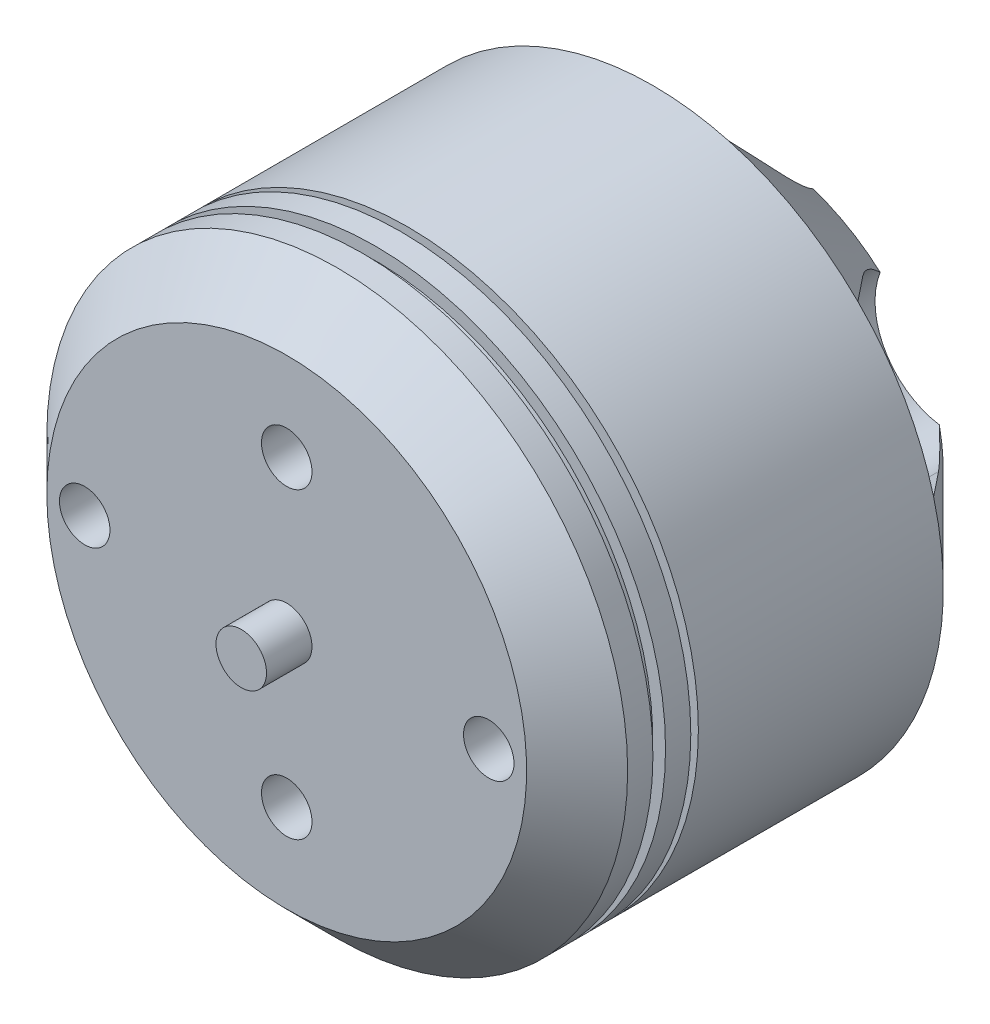
SolidWorks part; units mm, degrees
ref_plane "Front Plane" through (0, 0, 0) normal (0, 0, 1) x (1, 0, 0)
ref_plane "Top Plane" through (0, 0, 0) normal (0, 1, 0) x (1, 0, 0)
ref_plane "Right Plane" through (0, 0, 0) normal (1, 0, 0) x (0, 0, -1)
sketch "Sketch2" plane through (0, 0, 0) normal (0, 1, 0) x (1, 0, 0)
  line L0 (0, 22) -> (0, -1.8)
  line L1 (0, -1.8) -> (1, -1.8)
  line L2 (1, -1.8) -> (1, 0)
  line L3 (1, 0) -> (9.5, 0)
  line L4 (9.5, 0) -> (11.5, 2)
  line L5 (11.5, 2) -> (11.5, 3)
  line L6 (11.5, 14.5) -> (7.5, 18.5)
  line L7 (7.5, 18.5) -> (1, 18.5)
  line L8 (1, 18.5) -> (1, 22)
  line L9 (1, 22) -> (0, 22)
  line L10 (2, 17.5) -> (7.0858, 17.5)
  line L11 (7.0858, 17.5) -> (10.5, 14.0858)
  line L12 (10.5, 14.0858) -> (10.5, 8.9941)
  line L13 (10.5, 8.9941) -> (1, 8.9941)
  line L14 (1, 8.9941) -> (1, 16.5)
  line L15 (1, 16.5) -> (2, 16.5)
  line L16 (2, 16.5) -> (2, 17.5)
  line L17 (11.5, 3) -> (11, 3)
  line L18 (11, 3) -> (11, 3.5)
  line L19 (11, 3.5) -> (11.5, 3.5)
  line L20 (11.5, 4.5) -> (9.5, 4.5)
  line L21 (9.5, 4.5) -> (9.5, 4.8)
  line L22 (9.5, 4.8) -> (11.5, 4.8)
  line L23 (11.5, 4.8) -> (11.5, 14.5)
  line L24 (11.5, 3.5) -> (11.5, 4.5)
  dimension "D1" = 23.8
  dimension "D2" = 1.8
  dimension "D3" = 45
  dimension "D4" = 2
  dimension "D5" = 11.5
  dimension "D6" = 1
  dimension "D7" = 1
  dimension "D8" = 45
  dimension "D9" = 3.5
  dimension "D10" = 1
  dimension "D11" = 1
  dimension "D12" = 1
  dimension "D13" = 1
  dimension "D14" = 1
  dimension "D15" = 1
  dimension "D16" = 4
  dimension "D17" = 0.5
  dimension "D18" = 0.5
  dimension "D19" = 0.3
  dimension "D20" = 2
  dimension "D21" = 1
  dimension "D22" = 1
  dimension "D23" = 8.9941
revolve "Revolve3" add sketch "Sketch2" angle 360 about L0
sketch "Sketch3" plane through (0, 0, -18.5) normal (0, 0, -1) x (-1, 0, 0)
  line L0 (0, 0) -> (0, 9) construction
  line L1 (-3, 9) -> (-3, 16.3813)
  line L2 (-3, 16.3813) -> (3, 16.3813)
  line L3 (3, 16.3813) -> (3, 9)
  line L4 (15.6866, 5.5926) -> (9.2942, 1.9019)
  line L5 (12.6866, 10.7887) -> (15.6866, 5.5926)
  line L6 (6.2942, 7.0981) -> (12.6866, 10.7887)
  line L7 (12.6866, -10.7887) -> (6.2942, -7.0981)
  line L8 (15.6866, -5.5926) -> (12.6866, -10.7887)
  line L9 (9.2942, -1.9019) -> (15.6866, -5.5926)
  line L10 (-3, -16.3813) -> (-3, -9)
  line L11 (3, -16.3813) -> (-3, -16.3813)
  line L12 (3, -9) -> (3, -16.3813)
  line L13 (-15.6866, -5.5926) -> (-9.2942, -1.9019)
  line L14 (-12.6866, -10.7887) -> (-15.6866, -5.5926)
  line L15 (-6.2942, -7.0981) -> (-12.6866, -10.7887)
  line L16 (-12.6866, 10.7887) -> (-6.2942, 7.0981)
  line L17 (-15.6866, 5.5926) -> (-12.6866, 10.7887)
  line L18 (-9.2942, 1.9019) -> (-15.6866, 5.5926)
  circle A0 centre (0, 0) radius 4.5 construction
  circle A1 centre (0, 4.5) radius 1
  circle A2 centre (0, 0) radius 4.5 construction
  circle A3 centre (4.5, 0) radius 1
  circle A4 centre (0, 0) radius 4.5 construction
  circle A5 centre (0, -4.5) radius 1
  circle A6 centre (0, 0) radius 4.5 construction
  circle A7 centre (-4.5, 0) radius 1
  arc A8 (-3, 9) -> (3, 9) centre (0, 9) ccw
  arc A9 (6.2942, 7.0981) -> (9.2942, 1.9019) centre (7.7942, 4.5) ccw
  arc A10 (9.2942, -1.9019) -> (6.2942, -7.0981) centre (7.7942, -4.5) ccw
  arc A11 (3, -9) -> (-3, -9) centre (0, -9) ccw
  arc A12 (-6.2942, -7.0981) -> (-9.2942, -1.9019) centre (-7.7942, -4.5) ccw
  arc A13 (-9.2942, 1.9019) -> (-6.2942, 7.0981) centre (-7.7942, 4.5) ccw
  point P18 (0, 0)
  point P47 (0, 0)
  dimension "D1" = 9
  dimension "D3" = 2
  dimension "D5" = 6
  dimension "D2" = 9
  dimension "D4" = 4
  dimension "D6" = 6
extrude "Cut-Extrude1" cut sketch "Sketch3" against normal blind 4
sketch "Sketch4" plane through (0, 0, 0) normal (0, 0, 1) x (1, 0, 0)
  circle A0 centre (0, 0) radius 8 construction
  circle A1 centre (0, 0) radius 6 construction
  circle A2 centre (0, 6) radius 1
  circle A3 centre (0, -6) radius 1
  circle A4 centre (8, 0) radius 1
  circle A5 centre (-8, 0) radius 1
  dimension "D1" = 16
  dimension "D2" = 12
  dimension "D3" = 2
extrude "Cut-Extrude2" cut sketch "Sketch4" against normal blind 3
